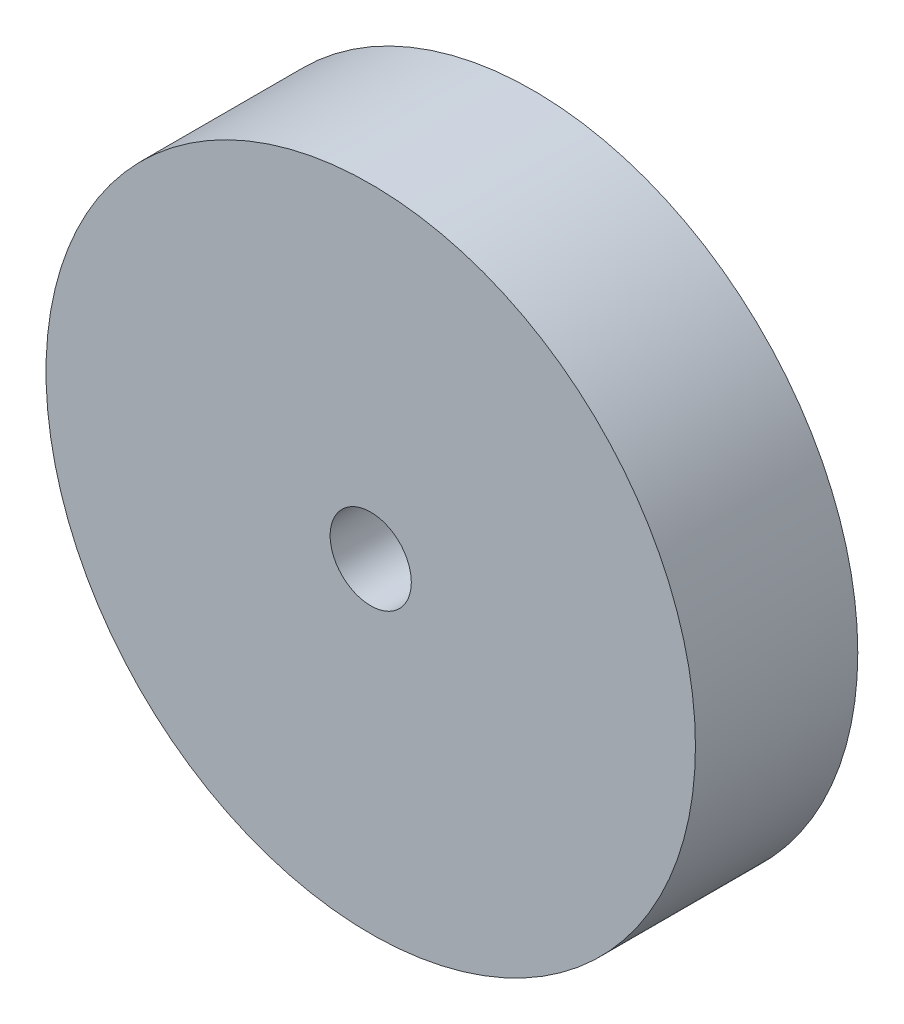
SolidWorks part; units mm, degrees
ref_plane "Plan de face" through (0, 0, 0) normal (0, 0, 1) x (1, 0, 0)
ref_plane "Plan de dessus" through (0, 0, 0) normal (0, 1, 0) x (1, 0, 0)
ref_plane "Plan de droite" through (0, 0, 0) normal (1, 0, 0) x (0, 0, -1)
sketch "Esquisse1" plane through (0, 0, 0) normal (0, 0, 1) x (1, 0, 0)
  circle A0 centre (0, 0) radius 10
  circle A1 centre (0, 0) radius 1.25
  dimension "D1" = 20
  dimension "D2" = 2.5
extrude "Boss.-Extru.1" add sketch "Esquisse1" along normal blind 5
